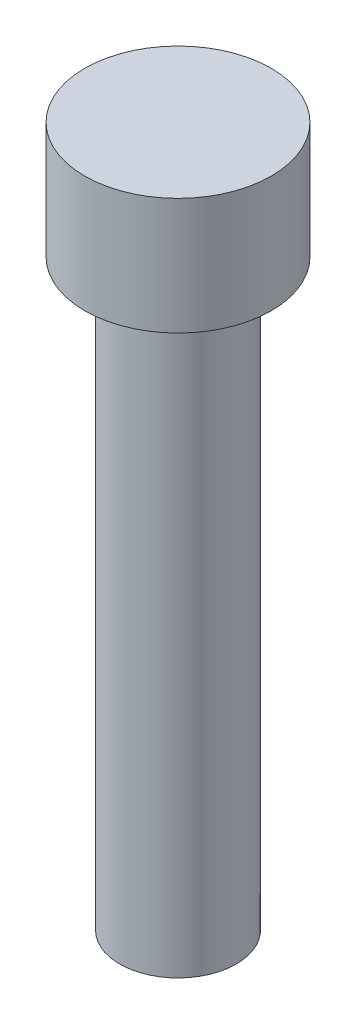
SolidWorks part; units mm, degrees
ref_plane "Front Plane" through (0, 0, 0) normal (0, 0, 1) x (1, 0, 0)
ref_plane "Top Plane" through (0, 0, 0) normal (0, 1, 0) x (1, 0, 0)
ref_plane "Right Plane" through (0, 0, 0) normal (1, 0, 0) x (0, 0, -1)
sketch "Sketch1" plane through (0, 0, 0) normal (0, 0, 1) x (1, 0, 0)
  line L0 (0, 0) -> (0, 30)
  line L1 (0, 30) -> (4, 30)
  line L2 (4, 30) -> (4, 25)
  line L3 (4, 25) -> (2.5, 25)
  line L4 (2.5, 25) -> (2.5, 0)
  line L5 (2.5, 0) -> (0, 0)
  dimension "D1" = 2.5
  dimension "D2" = 30
  dimension "D3" = 5
  dimension "D4" = 4
revolve "Revolve1" add sketch "Sketch1" angle 360 about L0
